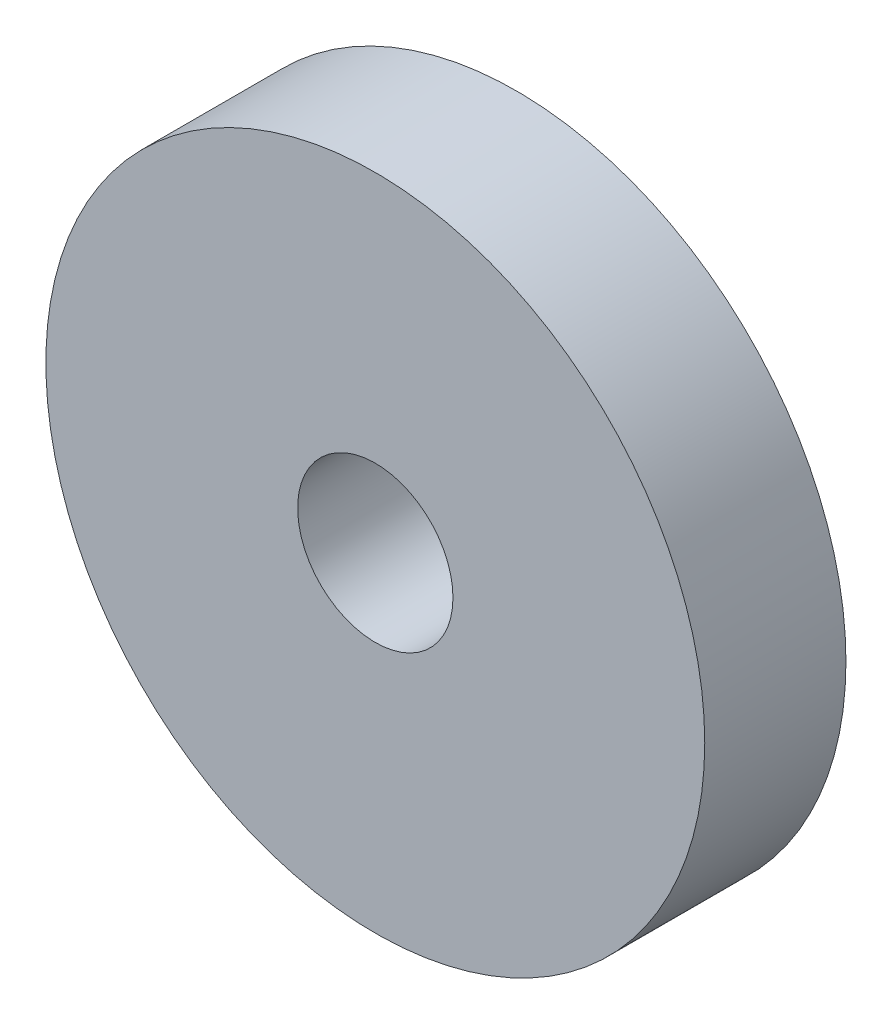
SolidWorks part; units mm, degrees
ref_plane "Front Plane" through (0, 0, 0) normal (0, 0, 1) x (1, 0, 0)
ref_plane "Top Plane" through (0, 0, 0) normal (0, 1, 0) x (1, 0, 0)
ref_plane "Right Plane" through (0, 0, 0) normal (1, 0, 0) x (0, 0, -1)
sketch "Sketch1" plane through (0, 0, 0) normal (0, 0, 1) x (1, 0, 0)
  circle A1 centre (0, 0) radius 7
extrude "Boss-Extrude1" add sketch "Sketch1" along normal blind 3
sketch "Sketch2" plane through (0, 0, 3) normal (0, 0, 1) x (1, 0, 0)
  circle A0 centre (0, 0) radius 1.65
extrude "Cut-Extrude1" cut sketch "Sketch2" against normal up to surface (3 mm away) up to face at (7, 0, 0)
